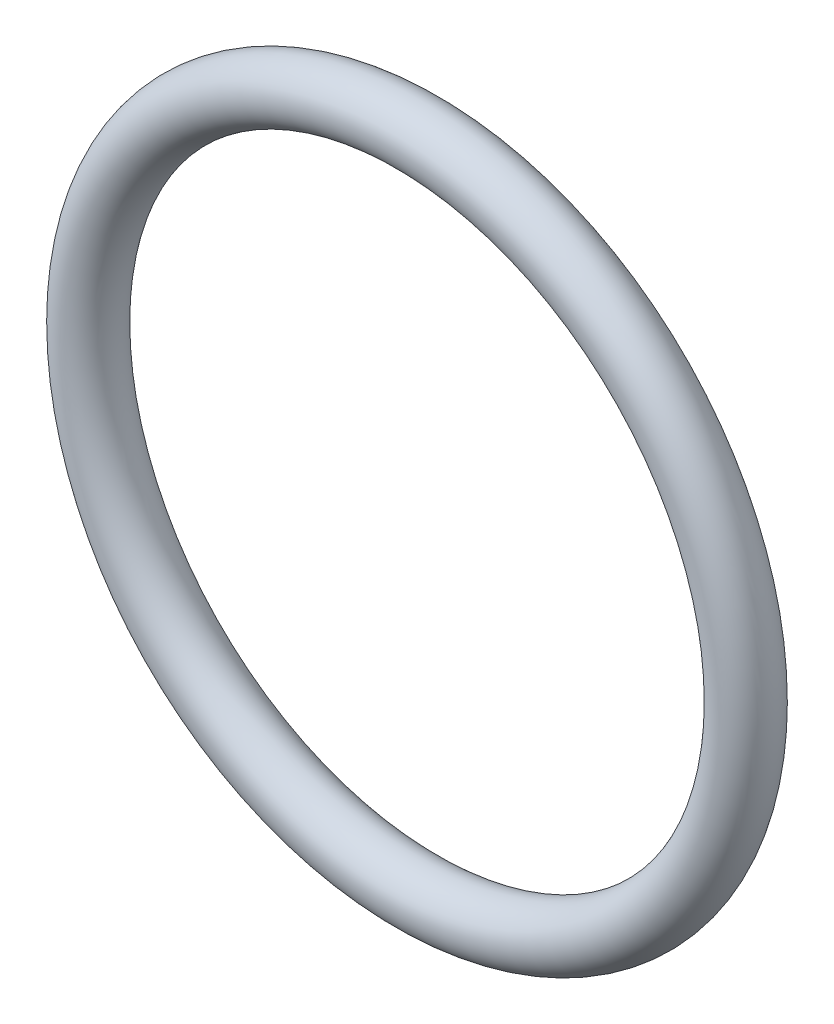
SolidWorks part; units mm, degrees
ref_plane "Front" through (0, 0, 0) normal (0, 0, 1) x (1, 0, 0)
ref_plane "Top" through (0, 0, 0) normal (0, 1, 0) x (1, 0, 0)
ref_plane "Right" through (0, 0, 0) normal (1, 0, 0) x (0, 0, -1)
sketch "Sketch1" plane through (0, 0, 0) normal (1, 0, 0) x (0, -1, 0)
  line L0 (0, -1.3081) -> (0, 1.3081) construction
  line L2 (-17.5323, 0) -> (17.5323, 0) construction
  line L3 (-13.3223, 0) -> (13.3223, 0) construction
  circle A0 centre (14.6304, 0) radius 1.3081
  point P9 (13.3223, 0)
  point P10 (15.9385, 0)
  point P13 (14.6304, 1.3081)
  point P14 (14.6304, -1.3081)
  dimension "Width" = 2.6162
  dimension "ID" = 26.6446
revolve "Revolve1" add sketch "Sketch1" angle 360 about L0
